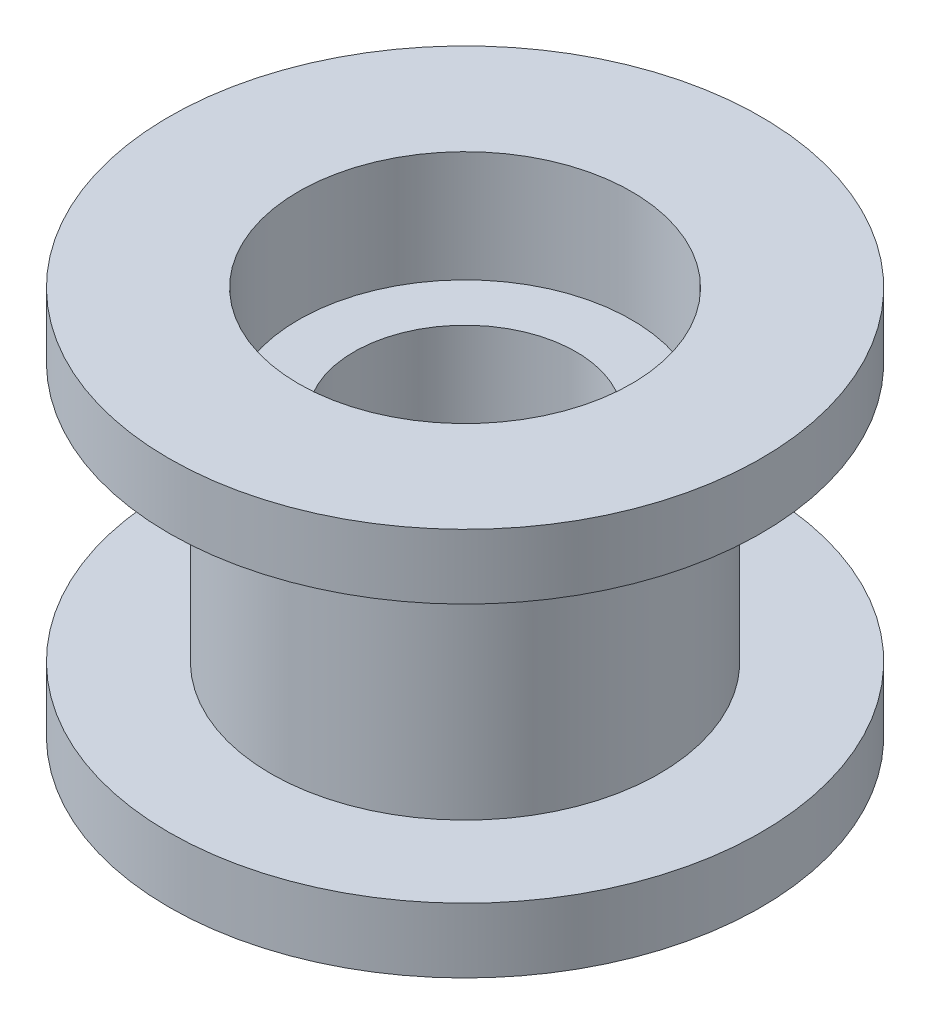
SolidWorks part; units mm, degrees
material "6061-T6 (SS)"
ref_plane "Front Plane" through (0, 0, 0) normal (0, 0, 1) x (1, 0, 0)
ref_plane "Top Plane" through (0, 0, 0) normal (0, 1, 0) x (1, 0, 0)
ref_plane "Right Plane" through (0, 0, 0) normal (1, 0, 0) x (0, 0, -1)
sketch "Sketch1" plane through (0, 0, 0) normal (0, 0, 1) x (1, 0, 0)
  line L0 (0, 0) -> (-4.5, 0) construction
  line L1 (-4.5, 0) -> (-8, 0)
  line L2 (-8, 0) -> (-8, -1.75)
  line L3 (-8, -1.75) -> (-5.25, -1.75)
  line L4 (-5.25, -1.75) -> (-5.25, -8.75)
  line L5 (-5.25, -5.25) -> (-3, -5.25) construction
  line L6 (-3, -7.5) -> (-3, -3)
  line L7 (-3, -3) -> (-4.5, -3)
  line L8 (-4.5, -3) -> (-4.5, 0)
  line L9 (0, 0) -> (0, -18.2286) construction
  line L10 (5.25, -1.75) -> (5.25, -8.75) construction
  line L11 (8, -1.75) -> (5.25, -1.75) construction
  line L12 (8, 0) -> (8, -1.75) construction
  line L13 (4.5, 0) -> (8, 0) construction
  line L14 (4.5, -3) -> (4.5, 0) construction
  line L15 (3, -3) -> (4.5, -3) construction
  line L16 (3, -7.5) -> (3, -3) construction
  line L17 (8, -8.75) -> (5.25, -8.75) construction
  line L18 (-8, -8.75) -> (-5.25, -8.75)
  line L19 (4.5, -7.5) -> (4.5, -10.5) construction
  line L20 (3, -7.5) -> (4.5, -7.5) construction
  line L21 (-3, -7.5) -> (-4.5, -7.5)
  line L22 (-4.5, -7.5) -> (-4.5, -10.5)
  line L23 (-4.5, -10.5) -> (-8, -10.5)
  line L24 (-8, -10.5) -> (-8, -8.75)
  line L25 (8, -10.5) -> (8, -8.75) construction
  line L26 (4.5, -10.5) -> (8, -10.5) construction
  point P20 (8, -0.875)
  point P21 (5.25, -5.25)
  point P26 (3, -5.25)
  dimension "D1" = 9
  dimension "D2" = 3
  dimension "D3" = 6
  dimension "D4" = 16
  dimension "D5" = 10.5
  dimension "D6" = 7
  dimension "D7" = 1.75
revolve "Revolve1" add sketch "Sketch1" angle 360 about L9
